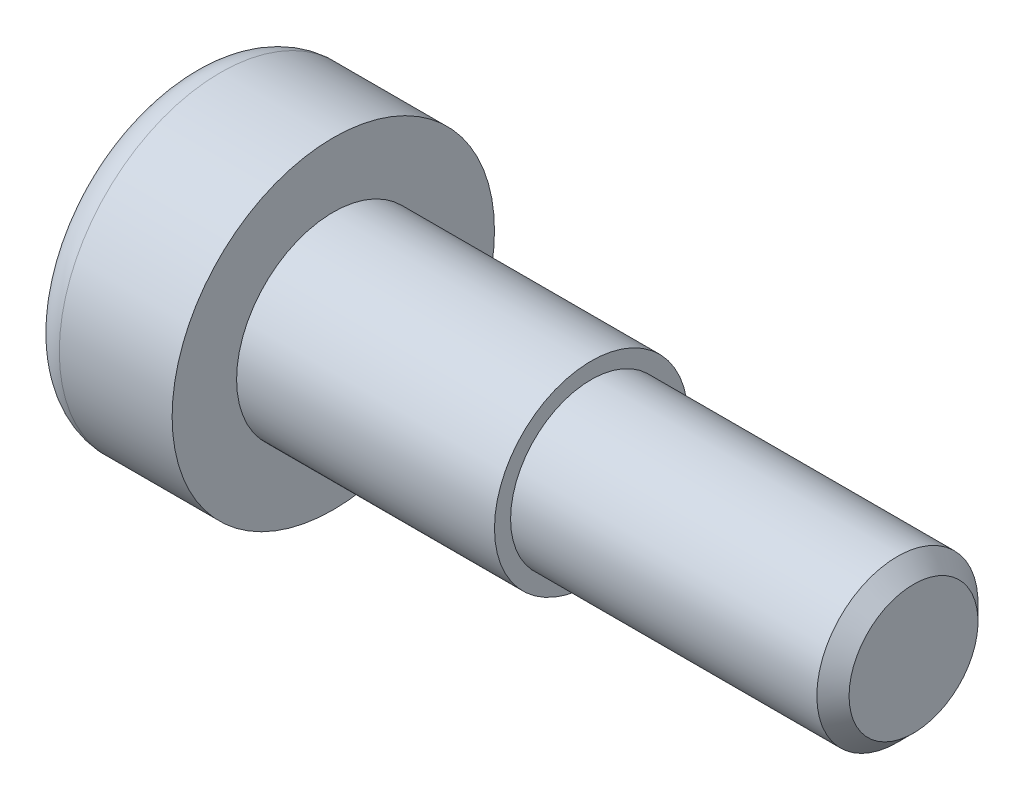
SolidWorks part; units mm, degrees
material "不锈钢 (铁素体)"
ref_plane "前视基准面" through (0, 0, 0) normal (0, 0, 1) x (1, 0, 0)
ref_plane "上视基准面" through (0, 0, 0) normal (0, 1, 0) x (1, 0, 0)
ref_plane "右视基准面" through (0, 0, 0) normal (1, 0, 0) x (0, 0, -1)
sketch "草图1" plane through (0, 0, 0) normal (0, 0, 1) x (1, 0, 0)
  line L0 (0, 0) -> (22.5, 0) construction
  line L1 (0, 0) -> (0, 5)
  line L2 (0, 5) -> (4.5, 5)
  line L3 (4.5, 5) -> (4.5, 3)
  line L4 (4.5, 3) -> (12.5, 3)
  line L5 (12.5, 3) -> (12.5, 2.5)
  line L6 (12.5, 2.5) -> (22.5, 2.5)
  line L7 (22.5, 2.5) -> (22.5, 0)
  line L8 (0, 0) -> (22.5, 0)
  dimension "D1" = 10
  dimension "D2" = 6
  dimension "D3" = 5
  dimension "D4" = 10
  dimension "D5" = 4.5
  dimension "D6" = 8
revolve "旋转1" add sketch "草图1" angle 360 about L0
cosmetic thread "装饰螺纹线1" parameters "D2"=4.134
sketch "草图2" plane through (0, 0, 0) normal (-1, 0, 0) x (0, 0, 1)
  line L0 (0, 0) -> (0, 1.7321) construction
  line L1 (0, 1.7321) -> (-1.5, 0.866)
  line L2 (-1.5, 0.866) -> (-1.5, -0.866)
  line L3 (-1.5, -0.866) -> (0, -1.7321)
  line L4 (0, -1.7321) -> (1.5, -0.866)
  line L5 (1.5, -0.866) -> (1.5, 0.866)
  line L6 (1.5, 0.866) -> (0, 1.7321)
  circle A0 centre (0, 0) radius 1.5 construction
  dimension "D1" = 3
extrude "切除-拉伸1" cut sketch "草图2" against normal blind 3
fillet "圆角1" radius 1 1 edges at (0, 0, 5)
chamfer "倒角1" distance 0.5 angle 45 1 edges at (22.5, 0, 2.5)
